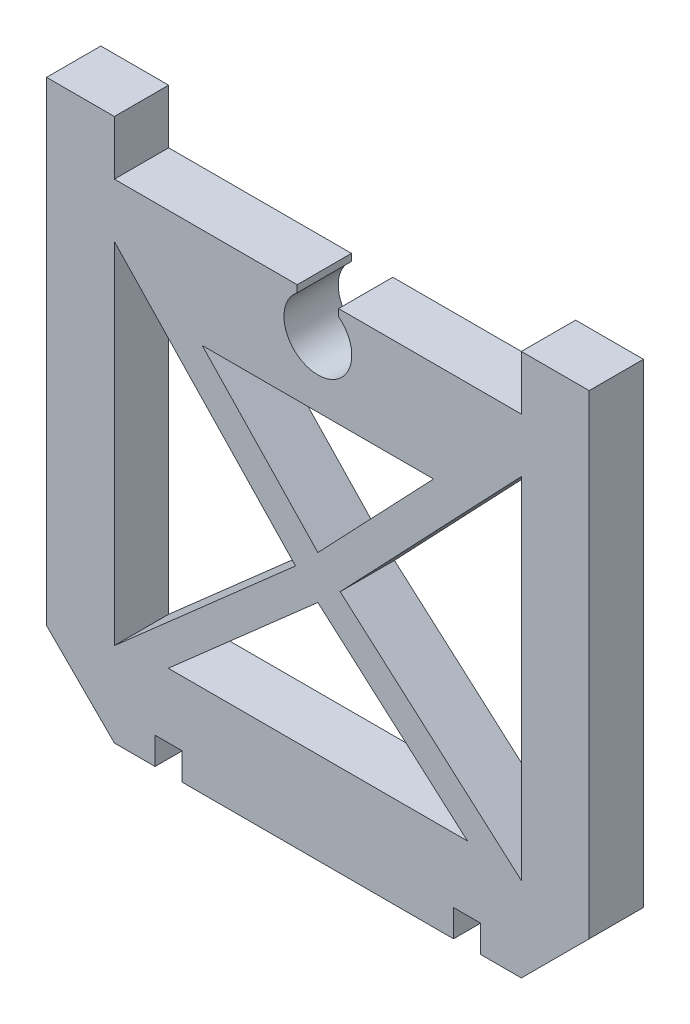
SolidWorks part; units mm, degrees
material "ﾊﾞﾙｻ"
ref_plane "正面" through (0, 0, 0) normal (0, 0, 1) x (1, 0, 0)
ref_plane "平面" through (0, 0, 0) normal (0, 1, 0) x (1, 0, 0)
ref_plane "右側面" through (0, 0, 0) normal (1, 0, 0) x (0, 0, -1)
sketch "ｽｹｯﾁ1" plane through (0, 0, 0) normal (0, 0, 1) x (1, 0, 0)
  line L0 (0, 0) -> (0, 2.5) construction
  line L1 (15, 2.5) -> (-15, 2.5)
  line L2 (-15, 2.5) -> (-15, 6.5)
  line L3 (-15, 6.5) -> (-20, 6.5)
  line L4 (-20, 6.5) -> (-20, -28.5)
  line L5 (-20, -28.5) -> (-15, -33.5)
  line L6 (-15, -33.5) -> (0, -33.5)
  line L7 (-12, -33.5) -> (-12, -31.5)
  line L8 (-12, -31.5) -> (-10, -31.5)
  line L9 (-10, -31.5) -> (-10, -33.5)
  line L10 (-15, -1.4819) -> (-15, -27.2797)
  line L11 (-15, -27.2797) -> (-1.6432, -15.5169)
  line L12 (-1.6432, -15.5169) -> (-15, -1.4819)
  line L13 (8.5261, -4.8804) -> (-8.5261, -4.8804)
  line L14 (-8.5261, -4.8804) -> (0, -13.8395)
  line L15 (0, -13.8395) -> (0, -4.8804) construction
  line L16 (0, -17.0262) -> (-11.0291, -26.7391)
  line L17 (-11.0291, -26.7391) -> (11.0291, -26.7391)
  line L18 (0, -26.7391) -> (0, -17.0262) construction
  line L19 (0, -33.5) -> (0, 2.5) construction
  line L20 (0, -17.0262) -> (11.0291, -26.7391)
  line L21 (8.5261, -4.8804) -> (0, -13.8395)
  line L22 (1.6432, -15.5169) -> (15, -1.4819)
  line L23 (15, -27.2797) -> (1.6432, -15.5169)
  line L24 (15, -1.4819) -> (15, -27.2797)
  line L25 (10, -31.5) -> (10, -33.5)
  line L26 (12, -31.5) -> (10, -31.5)
  line L27 (12, -33.5) -> (12, -31.5)
  line L28 (15, -33.5) -> (0, -33.5)
  line L29 (20, -28.5) -> (15, -33.5)
  line L30 (20, 6.5) -> (20, -28.5)
  line L31 (15, 6.5) -> (20, 6.5)
  line L32 (15, 2.5) -> (15, 6.5)
  line L33 (-1.5235, 2.5) -> (-1.5235, 1.9822)
  line L34 (1.5235, 2.5) -> (1.5235, 1.9822)
  circle A0 centre (0, 0) radius 2.5
  point P12 (-7.5, -33.5)
  dimension "D1" = 5
  dimension "D2" = 20
  dimension "D3" = 15
  dimension "D4" = 135
  dimension "D5" = 36
  dimension "D6" = 4
  dimension "D7" = 5
  dimension "D8" = 2
  dimension "D9" = 2
  dimension "D10" = 10
extrude "ﾎﾞｽ - 押し出し3" add sketch "ｽｹｯﾁ1" along normal blind 4 contours A0 L33 L1 L2 L3 L4 L5 L6 L7 L8 L9 L28 L25 L26 L27 L29 L30 L31 L32 L34 L12 L11 L10 L16 L20 L17 L13 L21 L14 L22 L24 L23
